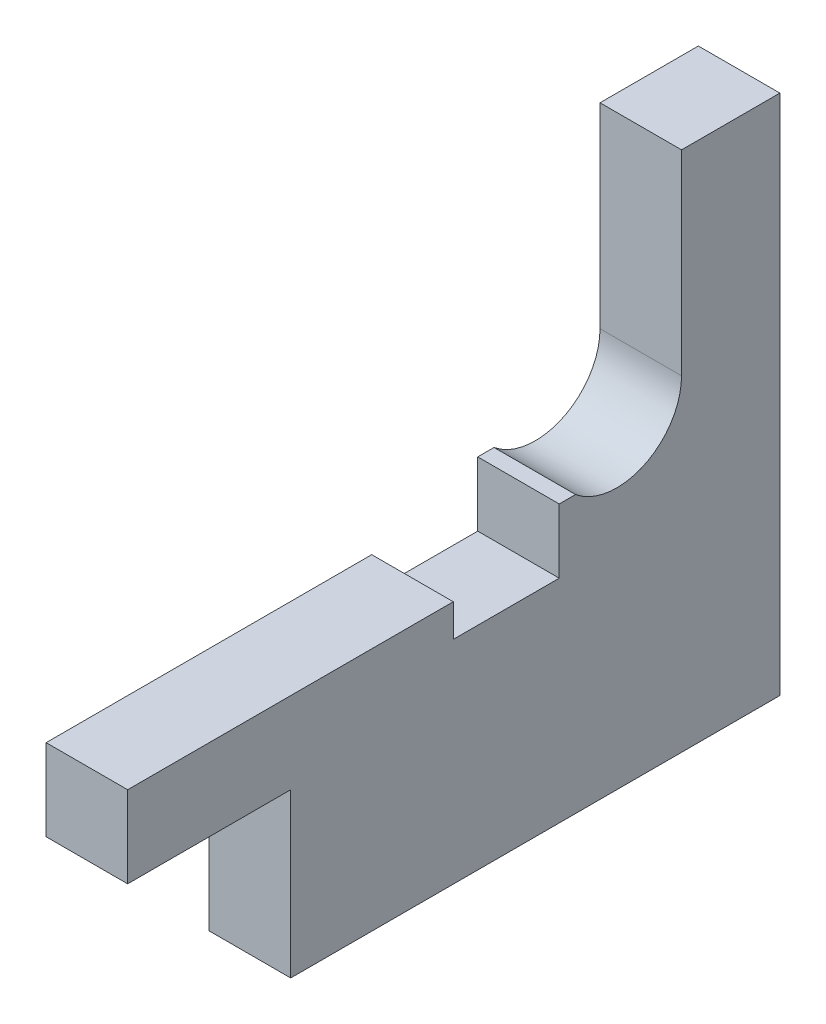
SolidWorks part; units mm, degrees
material "Plain Carbon Steel"
ref_plane "Front Plane" through (0, 0, 0) normal (0, 0, 1) x (1, 0, 0)
ref_plane "Top Plane" through (0, 0, 0) normal (0, 1, 0) x (1, 0, 0)
ref_plane "Right Plane" through (0, 0, 0) normal (1, 0, 0) x (0, 0, -1)
sketch "Sketch1" plane through (0, 0, 0) normal (1, 0, 0) x (0, 0, -1)
  line L0 (3.9688, 0) -> (3.9688, 12)
  line L1 (3.9688, 12) -> (10, 12)
  line L2 (10, 12) -> (10, -20)
  line L3 (10, -20) -> (-20, -20)
  line L4 (-20, -20) -> (-20, -10)
  line L5 (-20, -10) -> (-30, -10)
  line L6 (-30, -10) -> (-30, -5)
  line L10 (-30, -5) -> (-10.0312, -5)
  line L11 (-10.0312, -5) -> (-10.0312, -7)
  line L12 (-10.0312, -7) -> (-3.5312, -7)
  line L15 (-3.5312, -7) -> (-3.5312, -3.0568)
  line L17 (-3.5312, -3.0568) -> (-2.5312, -3.0568)
  arc A0 (-2.5312, -3.0568) -> (3.9688, 0) centre (0, 0) ccw
  dimension "D1" = 3.9688
  dimension "D2" = 30
  dimension "D3" = 32
  dimension "D4" = 5
  dimension "D5" = 10
  dimension "D6" = 10
  dimension "D7" = 12
  dimension "D8" = 10
  dimension "D9" = 1
  dimension "D10" = 6.5
  dimension "D11" = 2
  dimension "D12" = 6.5
extrude "Boss-Extrude1" add sketch "Sketch1" along normal blind 5 contours A0 L0 L1 L2 L3 L4 L5 L6 L10 L11 L12 L15 L17
